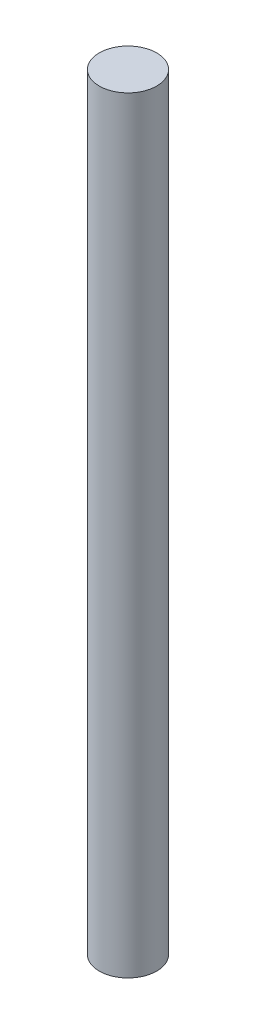
SolidWorks part; units mm, degrees
material "Chromium Copper, UNS C18200"
ref_plane "Front Plane" through (0, 0, 0) normal (0, 0, 1) x (1, 0, 0)
ref_plane "Top Plane" through (0, 0, 0) normal (0, 1, 0) x (1, 0, 0)
ref_plane "Right Plane" through (0, 0, 0) normal (1, 0, 0) x (0, 0, -1)
sketch "Sketch1" plane through (0, 0, 0) normal (0, 1, 0) x (1, 0, 0)
  circle A0 centre (0, 0) radius 1.8034
  dimension "D1" = 3.6068
extrude "Boss-Extrude1" add sketch "Sketch1" along normal blind 48.1076
cosmetic thread "Cosmetic Thread1" parameters "D1"=4.7625, "D2"=2.5603
cosmetic thread "Cosmetic Thread2" parameters "D1"=6.35, "D2"=2.5603
